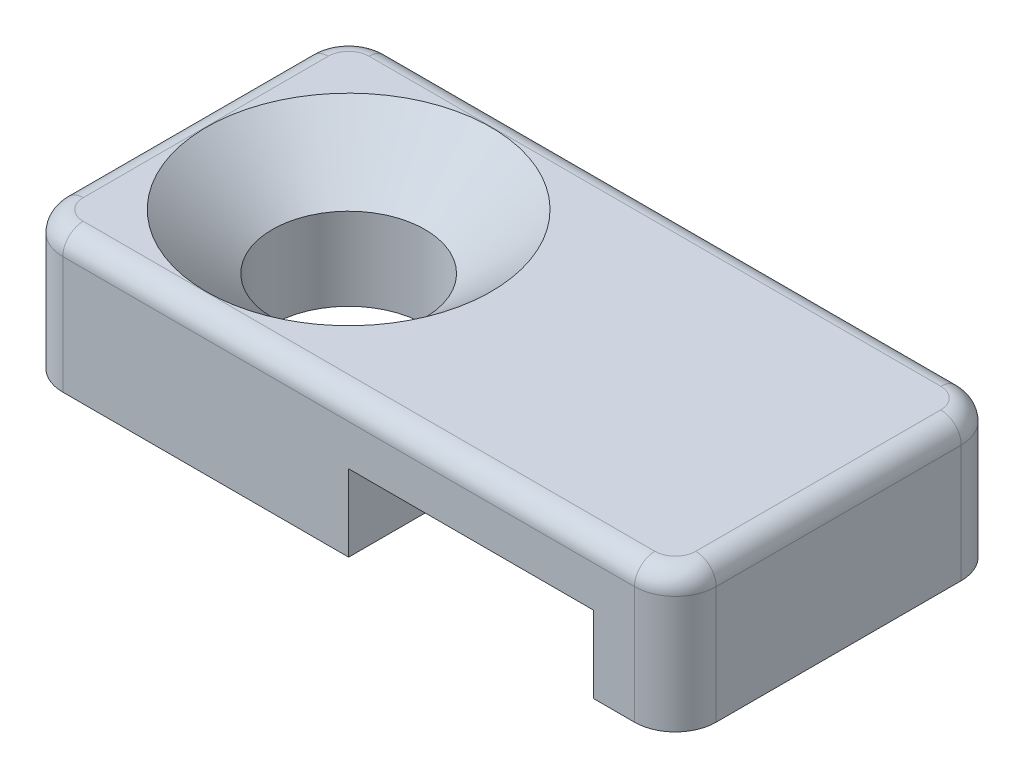
SolidWorks part; units mm, degrees
ref_plane "Front Plane" through (0, 0, 0) normal (0, 0, 1) x (1, 0, 0)
ref_plane "Top Plane" through (0, 0, 0) normal (0, 1, 0) x (1, 0, 0)
ref_plane "Right Plane" through (0, 0, 0) normal (1, 0, 0) x (0, 0, -1)
sketch "Sketch1" plane through (0, 0, 0) normal (0, 0, 1) x (1, 0, 0)
  line L5 (0, 0) -> (6.096, 0) construction
  line L6 (0, 0) -> (0, 1.905)
  line L7 (0, 1.905) -> (6.096, 1.905)
  line L8 (6.096, 0) -> (6.096, 1.905)
  line L10 (0, 0) -> (-8.128, 0)
  line L11 (-8.128, 0) -> (-8.128, 3.429)
  line L12 (-8.128, 3.429) -> (8.128, 3.429)
  line L13 (8.128, 3.429) -> (8.128, 0)
  line L14 (8.128, 0) -> (6.096, 0)
  dimension "D1" = 8.128
  dimension "D2" = 1.905
  dimension "D3" = 6.096
  dimension "D4" = 2.032
  dimension "D5" = 1.524
extrude "Boss-Extrude1" add sketch "Sketch1" along normal mid plane 8.128
hole_wizard "CSK for #6 Flat Head Machine Screw (100)1" positions "Sketch2" profile "Sketch3" countersink size "#6" standard "ANSI Inch" end condition through all
sketch "Sketch2" plane through (0, 3.429, 0) normal (0, 1, 0) x (1, 0, 0)
  line L0 (0, 0) -> (-4.064, 0) construction
  line L2 (-4.064, -4.064) -> (-4.064, 0) construction
  line L4 (-8.128, -4.064) -> (0, -4.064) construction
  point P0 (-4.064, 0)
  point P13 (-4.064, -4.064)
sketch "Sketch3" plane through (-4.064, 3.429, 0) normal (1, 0, 0) x (0, 0, 1)
  line L0 (0, 0) -> (0, 3.429)
  line L1 (0, 3.429) -> (1.8986, 3.429)
  line L2 (1.8986, 3.429) -> (1.8986, 1.38)
  line L3 (1.8986, 1.38) -> (3.5433, 0)
  line L5 (3.5433, 0) -> (0, 0)
  line L6 (-1.8986, 1.38) -> (-3.5433, 0) construction
  line L11 (0, -6.35) -> (0, 107.95) construction
  dimension "Thru Hole Dia." = 3.7973
  dimension "Thru Hole Depth" = 3.429
  dimension "Near C'Sink Dia." = 7.0866
  dimension "Near C'Sink Angle" = 100
fillet "Fillet1" radius 1.016 4 edges at (8.128, 1.7145, -4.064) (8.128, 1.7145, 4.064) (-8.128, 1.7145, -4.064) (-8.128, 1.7145, 4.064)
fillet "Fillet2" radius 0.508 8 edges at (7.8304, 3.429, 3.7664) (0, 3.429, 4.064) (-7.8304, 3.429, 3.7664) (-8.128, 3.429, 0) (-7.8304, 3.429, -3.7664) (0, 3.429, -4.064) (7.8304, 3.429, -3.7664) (8.128, 3.429, 0)
